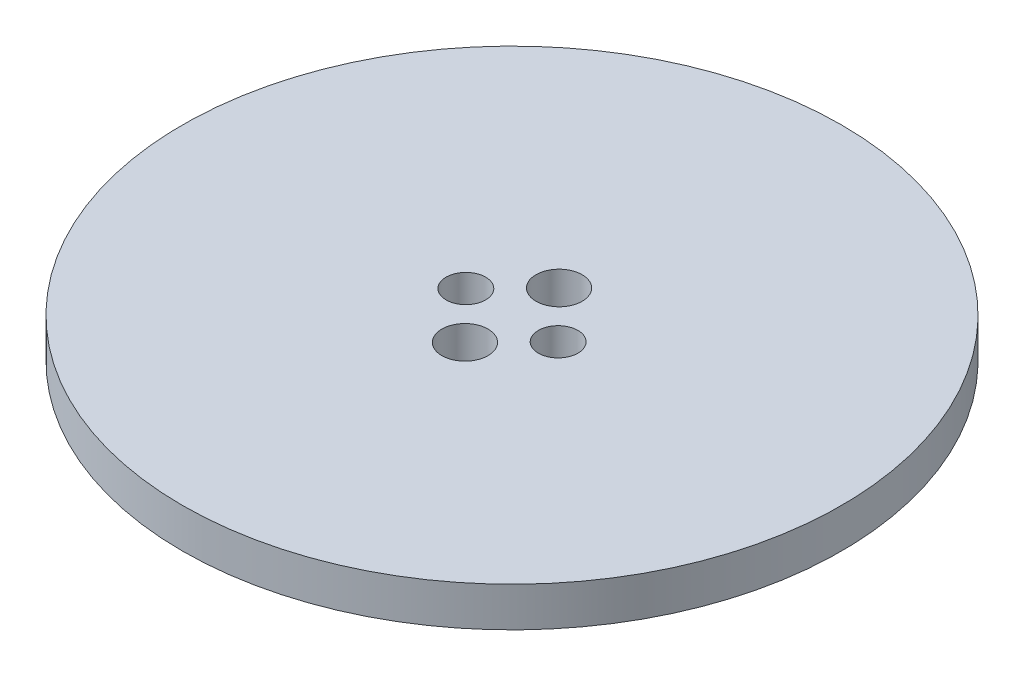
SolidWorks part; units mm, degrees
ref_plane "Plan de face" through (0, 0, 0) normal (0, 0, 1) x (1, 0, 0)
ref_plane "Plan de dessus" through (0, 0, 0) normal (0, 1, 0) x (1, 0, 0)
ref_plane "Plan de droite" through (0, 0, 0) normal (1, 0, 0) x (0, 0, -1)
sketch "Esquisse1" plane through (0, 0, 0) normal (0, 1, 0) x (1, 0, 0)
  line L0 (-3.5, 0) -> (0.25, 0) construction
  line L1 (2, 0) -> (3.5, 0) construction
  circle A0 centre (0, 0) radius 25
  circle A2 centre (-3.5, 0) radius 1.5
  circle A3 centre (3.5, 0) radius 1.5
  arc A10 (-1.9911, 2.8785) -> (-1.9911, -2.8785) centre (-3.5, 0) ccw construction
  circle A12 centre (0, 3.5707) radius 1.75
  circle A13 centre (0, -3.5707) radius 1.75
  dimension "D1" = 50
  dimension "D2" = 6.5
  dimension "D4" = 7
  dimension "D5" = 3
  dimension "D6" = 3
  dimension "D12" = 3.5
  dimension "D13" = 3.5
extrude "Boss.-Extru.1" add sketch "Esquisse1" along normal blind 3
